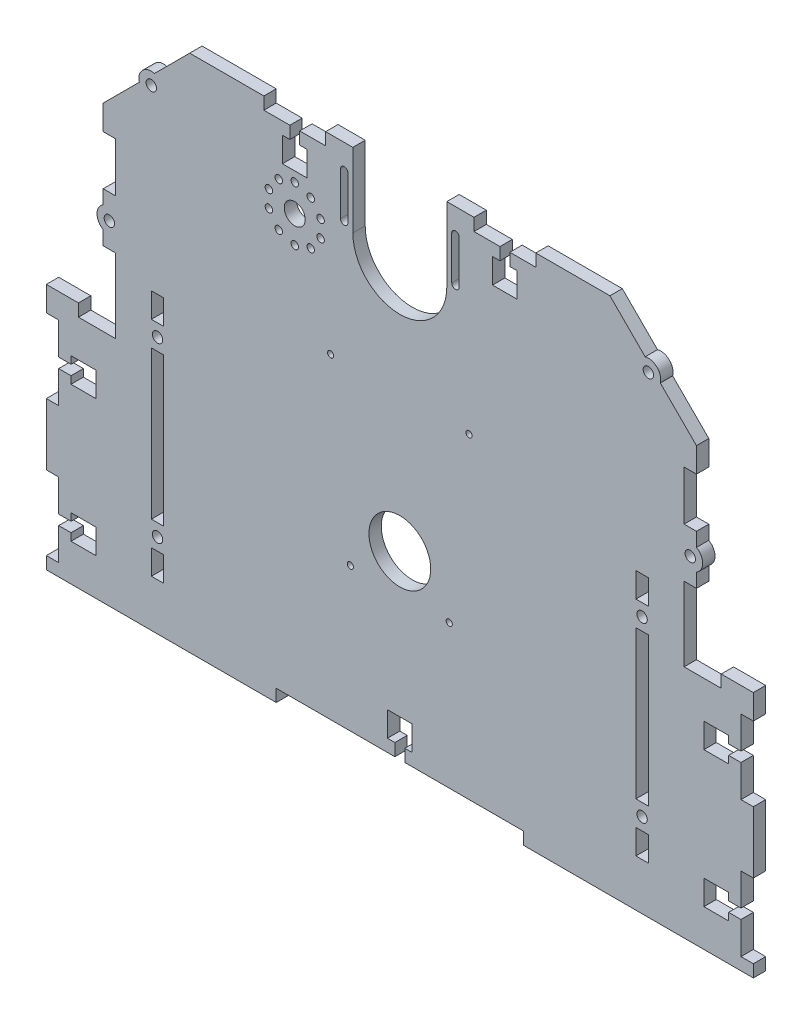
SolidWorks part; units mm, degrees
ref_plane "Front Plane" through (0, 0, 0) normal (0, 0, 1) x (1, 0, 0)
ref_plane "Top Plane" through (0, 0, 0) normal (0, 1, 0) x (1, 0, 0)
ref_plane "Right Plane" through (0, 0, 0) normal (1, 0, 0) x (0, 0, -1)
sketch "Sketch1" plane through (0, 0, 0) normal (0, 0, 1) x (1, 0, 0)
  line L1 (0, 0) -> (-240, 0)
  line L2 (0, 0) -> (0, 210)
  line L3 (0, 210) -> (-240, 210)
  line L4 (-240, 0) -> (-240, 210)
  dimension "D1" = 210
  dimension "D2" = 240
extrude "Boss-Extrude1" add sketch "Sketch1" along normal blind 5
sketch "Sketch2" plane through (0, 0, 5) normal (0, 0, 1) x (1, 0, 0)
  line L1 (-215.5, 19) -> (-220.5, 19)
  line L2 (-215.5, 19) -> (-215.5, 29)
  line L3 (-215.5, 29) -> (-220.5, 29)
  line L4 (-220.5, 19) -> (-220.5, 29)
  line L5 (-215.5, 39) -> (-220.5, 39)
  line L6 (-215.5, 39) -> (-215.5, 99)
  line L7 (-215.5, 99) -> (-220.5, 99)
  line L8 (-220.5, 39) -> (-220.5, 99)
  line L9 (-215.5, 109) -> (-220.5, 109)
  line L10 (-215.5, 109) -> (-215.5, 119)
  line L11 (-215.5, 119) -> (-220.5, 119)
  line L12 (-220.5, 109) -> (-220.5, 119)
  line L13 (-240, 210) -> (-240, 0) construction
  line L14 (-240, 0) -> (0, 0) construction
  line L15 (-200.5, 19) -> (-200.5, 29)
  line L16 (-200.5, 19) -> (-205.5, 19)
  line L17 (-205.5, 19) -> (-205.5, 29)
  line L18 (-200.5, 29) -> (-205.5, 29)
  line L19 (-200.5, 39) -> (-200.5, 99)
  line L20 (-205.5, 39) -> (-205.5, 99)
  line L21 (-200.5, 39) -> (-205.5, 39)
  line L22 (-200.5, 99) -> (-205.5, 99)
  line L23 (-200.5, 109) -> (-200.5, 119)
  line L24 (-200.5, 109) -> (-205.5, 109)
  line L25 (-205.5, 109) -> (-205.5, 119)
  line L26 (-200.5, 119) -> (-205.5, 119)
  line L27 (-120, 0) -> (-120, 45.6078) construction
  line L28 (-39.5, 119) -> (-34.5, 119)
  line L29 (-34.5, 109) -> (-34.5, 119)
  line L30 (-39.5, 109) -> (-34.5, 109)
  line L31 (-39.5, 109) -> (-39.5, 119)
  line L32 (-39.5, 99) -> (-34.5, 99)
  line L33 (-39.5, 39) -> (-34.5, 39)
  line L34 (-34.5, 39) -> (-34.5, 99)
  line L35 (-39.5, 39) -> (-39.5, 99)
  line L36 (-39.5, 29) -> (-34.5, 29)
  line L37 (-34.5, 19) -> (-34.5, 29)
  line L38 (-39.5, 19) -> (-34.5, 19)
  line L39 (-39.5, 19) -> (-39.5, 29)
  line L40 (-19.5, 109) -> (-19.5, 119)
  line L41 (-24.5, 119) -> (-19.5, 119)
  line L42 (-24.5, 109) -> (-24.5, 119)
  line L43 (-24.5, 109) -> (-19.5, 109)
  line L44 (-19.5, 39) -> (-19.5, 99)
  line L45 (-24.5, 99) -> (-19.5, 99)
  line L46 (-24.5, 39) -> (-24.5, 99)
  line L47 (-24.5, 39) -> (-19.5, 39)
  line L48 (-19.5, 19) -> (-19.5, 29)
  line L49 (-24.5, 29) -> (-19.5, 29)
  line L50 (-24.5, 19) -> (-24.5, 29)
  line L51 (-24.5, 19) -> (-19.5, 19)
  dimension "D1" = 5
  dimension "D2" = 10
  dimension "D3" = 60
  dimension "D4" = 10
  dimension "D5" = 5
  dimension "D6" = 5
  dimension "D7" = 19.5
  dimension "D8" = 119
  dimension "D9" = 10
  dimension "D10" = 10
  dimension "D11" = 2
extrude "Cut-Extrude1" cut sketch "Sketch2" against normal blind 5
sketch "Sketch3" plane through (0, 0, 5) normal (0, 0, 1) x (1, 0, 0)
  line L0 (-240, 210) -> (-240, 0) construction
  line L1 (0, 210) -> (-240, 210) construction
  line B0 (-120, 210) -> (-120, 177.73) construction
  line B1 (-240, 205) -> (-240, 185)
  line B2 (-240, 205) -> (-235, 205)
  line B3 (-240, 185) -> (-235, 185)
  line B4 (-235, 205) -> (-235, 185)
  line B5 (-240, 165) -> (-240, 145)
  line B6 (-240, 165) -> (-235, 165)
  line B7 (-235, 165) -> (-235, 145)
  line B8 (-240, 145) -> (-235, 145)
  line B9 (-235, 125) -> (-240, 125)
  line B10 (-235, 125) -> (-235, 100)
  line B11 (-235, 100) -> (-240, 100)
  line B12 (-240, 125) -> (-240, 100)
  line B13 (0, 125) -> (0, 100)
  line B14 (-5, 100) -> (0, 100)
  line B15 (-5, 125) -> (-5, 100)
  line B16 (-5, 125) -> (0, 125)
  line B17 (0, 145) -> (-5, 145)
  line B18 (-5, 165) -> (-5, 145)
  line B19 (0, 165) -> (-5, 165)
  line B20 (0, 165) -> (0, 145)
  line B21 (-5, 205) -> (-5, 185)
  line B22 (0, 185) -> (-5, 185)
  line B23 (0, 205) -> (-5, 205)
  line B24 (0, 205) -> (0, 185)
  dimension "D1" = 5
  dimension "D2" = 5
sketch_block_instance "Block2-1"
sketch_block "Block2" parameters "D1"=5, "D2"=20, "D3"=25, "D4"=20, "D5"=20, "D6"=5
extrude "Cut-Extrude2" cut sketch "Sketch3" against normal blind 10
sketch "Sketch4" plane through (0, 0, 5) normal (0, 0, 1) x (1, 0, 0)
  line L3 (0, 210) -> (-240, 210) construction
  line L5 (-120, 210) -> (-120, 170.8139) construction
  line L9 (-210, 205) -> (-235, 205)
  line L10 (-235, 205) -> (-235, 180)
  line L11 (-235, 180) -> (-210, 205)
  line L12 (-240, 185) -> (-240, 165) construction
  line L13 (-210, 205) -> (-205, 210)
  line L14 (-205, 210) -> (-240, 210)
  line L15 (-240, 210) -> (-240, 175)
  line L16 (-235, 180) -> (-240, 175)
  line L17 (-5, 180) -> (0, 175)
  line L18 (0, 210) -> (0, 175)
  line L19 (-35, 210) -> (0, 210)
  line L20 (-30, 205) -> (-35, 210)
  line L21 (-5, 180) -> (-30, 205)
  line L22 (-5, 205) -> (-5, 180)
  line L23 (-30, 205) -> (-5, 205)
  dimension "D1" = 25
  dimension "D2" = 25
  dimension "D3" = 5
  dimension "D4" = 5
extrude "Cut-Extrude3" cut sketch "Sketch4" against normal blind 10 contours L16 L10 L9 L13 L14 L15 | L10 L11 L9 | L23 L21 L22 | L20 L23 L22 L17 L18 L19
sketch "Sketch5" plane through (0, 0, 5) normal (0, 0, 1) x (1, 0, 0)
  line L0 (-35, 210) -> (-205, 210) construction
  line L1 (-175, 210) -> (-150, 210)
  line L2 (-175, 210) -> (-175, 205)
  line L3 (-175, 205) -> (-150, 205)
  line L4 (-150, 210) -> (-150, 205)
  line L5 (-120, 210) -> (-120, 191.0501) construction
  line L6 (-65, 205) -> (-90, 205)
  line L7 (-90, 210) -> (-90, 205)
  line L8 (-65, 210) -> (-90, 210)
  line L9 (-65, 210) -> (-65, 205)
  dimension "D1" = 5
  dimension "D2" = 25
  dimension "D3" = 30
extrude "Cut-Extrude4" cut sketch "Sketch5" against normal blind 10
sketch "Sketch7" plane through (0, 0, 5) normal (0, 0, 1) x (1, 0, 0)
  line L0 (-205.5, 39) -> (-200.5, 39) construction
  line L1 (-200.5, 39) -> (-200.5, 99) construction
  line L2 (-203, 34) -> (-218, 34) construction
  line L3 (-210.5, 34) -> (-210.5, 46.7899) construction
  line L4 (-215.5, 69) -> (-205.5, 69) construction
  line L5 (-215.5, 39) -> (-215.5, 99) construction
  line L6 (-205.5, 99) -> (-205.5, 39) construction
  line L7 (-120, 0) -> (-120, 30.8052) construction
  line L8 (-240, 0) -> (0, 0) construction
  line L9 (-24.5, 69) -> (-34.5, 69) construction
  line L10 (-29.5, 34) -> (-29.5, 46.7899) construction
  line L11 (-37, 34) -> (-22, 34) construction
  circle A0 centre (-203, 34) radius 2.1
  circle A1 centre (-218, 34) radius 2.1
  circle A2 centre (-203, 104) radius 2.1
  circle A3 centre (-218, 104) radius 2.1
  circle A4 centre (-22, 104) radius 2.1
  circle A5 centre (-37, 104) radius 2.1
  circle A6 centre (-22, 34) radius 2.1
  circle A7 centre (-37, 34) radius 2.1
  dimension "D1" = 4.2
  dimension "D2" = 5
  dimension "D3" = 2.5
extrude "Cut-Extrude6" cut sketch "Sketch7" against normal blind 5
sketch "Sketch8" plane through (0, 0, 5) normal (0, 0, 1) x (1, 0, 0)
  line L0 (-124.3301, 210) -> (-115.6699, 210)
  line L2 (-54.3301, 210) -> (-45.6699, 210)
  line L3 (-194.3301, 210) -> (-185.6699, 210)
  line L4 (0, 0) -> (0, 100) construction
  line L5 (-240, 0) -> (0, 0) construction
  arc A1 (-115.6699, 210) -> (-124.3301, 210) centre (-120, 207.5) ccw
  arc A2 (-45.6699, 210) -> (-54.3301, 210) centre (-50, 207.5) ccw
  arc A3 (-185.6699, 210) -> (-194.3301, 210) centre (-190, 207.5) ccw
  dimension "D1" = 45.6699
  dimension "D2" = 10
  dimension "D3" = 50
  dimension "D4" = 115.6699
  dimension "D5" = 185.6699
  dimension "D6" = 207.5
extrude "Boss-Extrude2" add sketch "Sketch8" against normal blind 5
sketch "Sketch9" plane through (0, 0, 5) normal (0, 0, 1) x (1, 0, 0)
  line L0 (-120, 212.5) -> (-120, 198.1441) construction
  circle A0 centre (-50, 207.5) radius 2.1
  arc A1 (-115.6699, 210) -> (-124.3301, 210) centre (-120, 207.5) ccw construction
  circle A2 centre (-120, 207.5) radius 2.1
  circle A3 centre (-190, 207.5) radius 2.1
  dimension "D1" = 4.2
  dimension "D2" = 4.2
extrude "Cut-Extrude7" cut sketch "Sketch9" against normal blind 5
sketch "Sketch10" plane through (0, 0, 5) normal (0, 0, 1) x (1, 0, 0)
  line L0 (-205, 210) -> (-240, 175) construction
  line L1 (-222.305, 192.695) -> (-212.586, 182.9761) construction
  line L2 (-115.6699, 210) -> (-124.3301, 210) construction
  line L3 (-120, 210) -> (-120, 185.6797) construction
  line L4 (-17.695, 192.695) -> (-27.414, 182.9761) construction
  circle A0 centre (-220.5372, 190.9273) radius 2.1
  circle A1 centre (-19.4628, 190.9273) radius 2.1
  dimension "D1" = 4.2
  dimension "D2" = 2.5
extrude "Cut-Extrude8" cut sketch "Sketch10" against normal blind 5
sketch "Sketch11" plane through (0, 0, 5) normal (0, 0, 1) x (1, 0, 0)
  line L0 (-205, 210) -> (-240, 175) construction
  line L1 (-219.2431, 195.7569) -> (-225.3668, 189.6332)
  line L2 (-90, 205) -> (-150, 205) construction
  line L3 (-120, 205) -> (-120, 186.0831) construction
  line L4 (-20.7569, 195.7569) -> (-14.6332, 189.6332)
  arc A0 (-219.2431, 195.7569) -> (-225.3668, 189.6332) centre (-220.5372, 190.9273) ccw
  arc A1 (-20.7569, 195.7569) -> (-14.6332, 189.6332) centre (-19.4628, 190.9273) cw
  dimension "D1" = 5
extrude "Boss-Extrude3" add sketch "Sketch11" against normal blind 5
sketch "Sketch13" plane through (0, 0, 5) normal (0, 0, 1) x (1, 0, 0)
  line L0 (-235, 125) -> (-240, 125) construction
  line L1 (-240, 145) -> (-240, 125) construction
  line L2 (-120, 207.5) -> (-120, 177.5095) construction
  circle A0 centre (-237.5, 135) radius 2.1
  circle A1 centre (-2.5, 135) radius 2.1
  dimension "D1" = 4.2
  dimension "D2" = 10
  dimension "D3" = 2.5
extrude "Cut-Extrude9" cut sketch "Sketch13" against normal blind 5
sketch "Sketch14" plane through (0, 0, 5) normal (0, 0, 1) x (1, 0, 0)
  line L0 (0, 0) -> (0, 100) construction
  line L1 (-240, 0) -> (0, 0) construction
  circle A4 centre (-92, 133) radius 1.25
  circle A5 centre (-100, 63) radius 1.25
  circle A6 centre (-148, 133) radius 1.25
  circle A7 centre (-140, 63) radius 1.25
  dimension "D1" = 2.5
  dimension "D2" = 92
  dimension "D3" = 100
  dimension "D4" = 140
  dimension "D5" = 148
  dimension "D6" = 63
  dimension "D7" = 133
extrude "Cut-Extrude10" cut sketch "Sketch14" against normal blind 5
sketch "Sketch22" plane through (0, 0, 5) normal (0, 0, 1) x (1, 0, 0)
  line L0 (-120, 209.6) -> (-120, 181.3792) construction
  line L1 (-124.3301, 210) -> (-150, 210) construction
  circle A0 centre (-120, 207.5) radius 2.1 construction
  circle A1 centre (-120, 180) radius 19
  dimension "D1" = 38
  dimension "D2" = 30
extrude "Cut-Extrude16" cut sketch "Sketch22" against normal blind 5
sketch "Sketch23" plane through (0, 0, 5) normal (0, 0, 1) x (1, 0, 0)
  line L1 (-240, 145) -> (-240, 125) construction
  line L2 (-240, 130.6699) -> (-240, 139.3301)
  line L3 (-120, 207.5) -> (-120, 197.1614) construction
  line L4 (0, 130.6699) -> (0, 139.3301)
  line L5 (0, 0) -> (0, 100) construction
  line L6 (-240, 0) -> (0, 0) construction
  arc A0 (-240, 139.3301) -> (-240, 130.6699) centre (-237.5, 135) ccw
  arc A1 (0, 139.3301) -> (0, 130.6699) centre (-2.5, 135) cw
  dimension "D1" = 5
  dimension "D2" = 2.5
  dimension "D3" = 130.6699
extrude "Boss-Extrude4" add sketch "Sketch23" against normal blind 5
sketch "Sketch26" plane through (0, 0, 5) normal (0, 0, 1) x (1, 0, 0)
  line L0 (0, 100) -> (23, 100)
  line L1 (0, 0) -> (0, 100) construction
  line L2 (23, 100) -> (23, -6)
  line L3 (23, -6) -> (-17, -6)
  line L4 (-17, -6) -> (-17, 0)
  line L5 (-240, 0) -> (0, 0) construction
  line L6 (0, 100) -> (0, 0)
  line L7 (0, 0) -> (-17, 0)
  line L8 (-120, 0) -> (-120, 18.176) construction
  line L9 (-240, 0) -> (-223, 0)
  line L10 (-240, 100) -> (-240, 0)
  line L11 (-223, -6) -> (-223, 0)
  line L12 (-263, -6) -> (-223, -6)
  line L13 (-263, 100) -> (-263, -6)
  line L14 (-240, 100) -> (-263, 100)
  line L15 (0, 0) -> (23, 0)
  line L16 (-240, 0) -> (-263, 0)
  dimension "D1" = 23
  dimension "D2" = 106
  dimension "D3" = 6
  dimension "D4" = 40
extrude "Boss-Extrude5" add sketch "Sketch26" against normal blind 5 contours L6 L15 L2 L0 | L16 L10 L14 L13
sketch "Sketch27" plane through (0, 0, 5) normal (0, 0, 1) x (1, 0, 0)
  line L1 (23, 90) -> (18, 90)
  line L2 (23, 90) -> (23, 60)
  line L3 (23, 60) -> (18, 60)
  line L4 (18, 90) -> (18, 60)
  line L6 (23, 35) -> (18, 35)
  line L7 (23, 35) -> (23, 5)
  line L8 (23, 5) -> (18, 5)
  line L9 (18, 35) -> (18, 5)
  line L10 (-263, 100) -> (-263, 0) construction
  line L11 (-120, 0) -> (-120, 32.5567) construction
  line L12 (-263, 0) -> (23, 0) construction
  line L13 (-258, 35) -> (-258, 5)
  line L14 (-263, 5) -> (-258, 5)
  line L15 (-263, 35) -> (-263, 5)
  line L16 (-263, 35) -> (-258, 35)
  line L17 (-258, 90) -> (-258, 60)
  line L18 (-263, 60) -> (-258, 60)
  line L19 (-263, 90) -> (-263, 60)
  line L20 (-263, 90) -> (-258, 90)
  line L21 (-263, 0) -> (23, 0) construction
  circle A0 centre (20.5, 47.5) radius 2.1
  circle A1 centre (-260.5, 47.5) radius 2.1
  dimension "D6" = 4.2
  dimension "D8" = 12.5
  dimension "D1" = 30
  dimension "D2" = 30
  dimension "D3" = 5
  dimension "D4" = 25
extrude "Cut-Extrude19" cut sketch "Sketch27" against normal blind 5 contours L20 L19 L18 L17 | L16 L15 L14 L13 | L1 L4 L3 L2 | L6 L9 L8 L7
sketch "Sketch28" plane through (0, 0, 5) normal (0, 0, 1) x (1, 0, 0)
  line L1 (23, 43.1699) -> (23, 51.8301)
  line L2 (-120, 0) -> (-120, 20.2272) construction
  line L3 (-263, 0) -> (23, 0) construction
  line L4 (-263, 43.1699) -> (-263, 51.8301)
  arc A0 (23, 51.8301) -> (23, 43.1699) centre (20.5, 47.5) cw
  arc A1 (-263, 51.8301) -> (-263, 43.1699) centre (-260.5, 47.5) ccw
  dimension "D1" = 5
extrude "Boss-Extrude6" [suppressed] add sketch "Sketch28" against normal blind 5
sketch "Sketch29" plane through (0, 0, 5) normal (0, 0, 1) x (1, 0, 0)
  line L0 (-120, 0) -> (-120, 23.9955) construction
  line L1 (-240, 95) -> (-235, 95)
  line L2 (-240, 95) -> (-240, 100)
  line L3 (-240, 100) -> (-235, 100)
  line L4 (-235, 95) -> (-235, 100)
  line L5 (-263, 0) -> (23, 0) construction
  line L6 (-5, 95) -> (-5, 100)
  line L7 (0, 100) -> (-5, 100)
  line L8 (0, 95) -> (0, 100)
  line L9 (0, 95) -> (-5, 95)
  dimension "D1" = 5
  dimension "D2" = 5
extrude "Cut-Extrude20" cut sketch "Sketch29" against normal blind 5
sketch "Sketch31" plane through (0, 100, 0) normal (0, 1, 0) x (1, 0, 0)
  line L1 (-240, 0) -> (-250, 0)
  line L2 (-240, 0) -> (-240, -5)
  line L3 (-240, -5) -> (-250, -5)
  line L4 (-250, 0) -> (-250, -5)
  dimension "D1" = 10
extrude "Cut-Extrude21" cut sketch "Sketch31" against normal blind 5
ref_plane "Plane1" through (-120, 0, 0) normal (-1, 0, 0) x (0, 0, 1)
mirror "Mirror2" about plane through (-120, 0, 0) normal (-1, 0, 0) of "Cut-Extrude21"
sketch "Sketch32" plane through (0, 0, 0) normal (0, -1, 0) x (1, 0, 0)
  line L4 (23, 5) -> (-263, 5)
  line L5 (23, 0) -> (23, 5)
  line L6 (-263, 0) -> (23, 0)
  line L8 (23, 5) -> (-263, 5)
  line L10 (-263, 0) -> (23, 0)
  line L16 (23, 0) -> (23, 5)
  line L18 (-263, 5) -> (-263, 0)
  line L19 (-263, 5) -> (-263, 0)
  dimension "D1" = 0
extrude "Boss-Extrude7" add sketch "Sketch32" along normal blind 1
sketch "Sketch33" plane through (0, -1, 0) normal (0, -1, 0) x (1, 0, 0)
  line L4 (23, 0) -> (23, 5)
  line L5 (23, 5) -> (-263, 5)
  line L6 (-263, 5) -> (-263, 0)
  line L7 (-263, 0) -> (23, 0)
  line L8 (23, 0) -> (23, 5)
  line L9 (23, 5) -> (-263, 5)
  line L10 (-263, 5) -> (-263, 0)
  line L11 (-263, 0) -> (23, 0)
  dimension "D1" = 0
extrude "Cut-Extrude22" cut sketch "Sketch33" against normal blind 1
sketch "Sketch35" plane through (0, 0, 5) normal (0, 0, 1) x (1, 0, 0)
  line L0 (18, 35) -> (18, 5) construction
  line L1 (18, 18) -> (13, 18)
  line L2 (18, 18) -> (18, 22)
  line L3 (18, 22) -> (13, 22)
  line L4 (13, 18) -> (13, 22)
  line L5 (-120, 0) -> (-120, 26.557) construction
  line L6 (13, 15) -> (3, 15)
  line L7 (13, 15) -> (13, 25)
  line L8 (13, 25) -> (3, 25)
  line L9 (3, 15) -> (3, 25)
  line L10 (23, 0) -> (-263, 0) construction
  line L11 (-243, 15) -> (-243, 25)
  line L12 (-253, 25) -> (-243, 25)
  line L13 (-253, 15) -> (-253, 25)
  line L14 (-253, 15) -> (-243, 15)
  line L15 (-253, 18) -> (-253, 22)
  line L16 (-258, 22) -> (-253, 22)
  line L17 (-258, 18) -> (-258, 22)
  line L18 (-258, 18) -> (-253, 18)
  line L19 (25.5, 47.5) -> (14.6629, 47.5) construction
  line L21 (-258, 77) -> (-253, 77)
  line L22 (-258, 77) -> (-258, 73)
  line L23 (-258, 73) -> (-253, 73)
  line L24 (-253, 77) -> (-253, 73)
  line L25 (-253, 80) -> (-243, 80)
  line L26 (-253, 80) -> (-253, 70)
  line L27 (-253, 70) -> (-243, 70)
  line L28 (-243, 80) -> (-243, 70)
  line L29 (3, 80) -> (3, 70)
  line L30 (13, 70) -> (3, 70)
  line L31 (13, 80) -> (13, 70)
  line L32 (13, 80) -> (3, 80)
  line L33 (13, 77) -> (13, 73)
  line L34 (18, 73) -> (13, 73)
  line L35 (18, 77) -> (18, 73)
  line L36 (18, 77) -> (13, 77)
  point P10 (13, 20)
  point P11 (18, 20)
  point P12 (18, 20)
  dimension "D1" = 5
  dimension "D2" = 5
  dimension "D3" = 10
  dimension "D4" = 10
  dimension "D5" = 4
extrude "Cut-Extrude24" cut sketch "Sketch35" against normal blind 5 contours L7 L1 L2 L3 | L9 L1 L7 L3 | L1 L9 L3 L4 | L9 L3 L7 L8 | L9 L6 L7 L1 | L31 L36 L29 L34 | L29 L36 L33 L34 | L36 L31 L32 L29 | L31 L34 L29 L30 | L35 L36 L31 L34 | L17 L18 L13 L16 | L13 L18 L11 L16 | L13 L16 L11 L12 | L18 L13 L14 L11 | L11 L18 L15 L16 | L28 L21 L26 L23 | L26 L21 L22 L23 | L28 L25 L26 L21 | L28 L23 L26 L27 | L21 L28 L23 L24
sketch "Sketch37" plane through (0, 0, 5) normal (0, 0, 1) x (1, 0, 0)
  line L0 (-194.3301, 210) -> (-185.6699, 210)
  line L1 (-124.3301, 210) -> (-115.6699, 210)
  line L2 (-54.3301, 210) -> (-45.6699, 210)
  arc A0 (-185.6699, 210) -> (-194.3301, 210) centre (-190, 207.5) ccw construction
  arc A1 (-115.6699, 210) -> (-124.3301, 210) centre (-120, 207.5) ccw construction
  arc A2 (-45.6699, 210) -> (-54.3301, 210) centre (-50, 207.5) ccw construction
  arc A3 (-185.6699, 210) -> (-194.3301, 210) centre (-190, 207.5) ccw
  arc A4 (-115.6699, 210) -> (-124.3301, 210) centre (-120, 207.5) ccw
  arc A5 (-45.6699, 210) -> (-54.3301, 210) centre (-50, 207.5) ccw
  circle A6 centre (-190, 207.5) radius 2.1
  circle A7 centre (-120, 207.5) radius 2.1
  circle A8 centre (-50, 207.5) radius 2.1
extrude "Cut-Extrude25" cut sketch "Sketch37" against normal blind 5
sketch "Sketch38" plane through (0, 0, 5) normal (0, 0, 1) x (1, 0, 0)
  circle A0 centre (-190, 207.5) radius 2.1 construction
  circle A1 centre (-120, 207.5) radius 2.1 construction
  circle A2 centre (-50, 207.5) radius 2.1 construction
  circle A3 centre (-190, 207.5) radius 2.1
  circle A4 centre (-120, 207.5) radius 2.1
  circle A5 centre (-50, 207.5) radius 2.1
extrude "Boss-Extrude8" add sketch "Sketch38" against normal blind 5
sketch "Sketch39" plane through (0, 0, 5) normal (0, 0, 1) x (1, 0, 0)
  line L0 (-175, 205) -> (-150, 205) construction
  line L1 (-160.5, 205) -> (-164.5, 205)
  line L2 (-160.5, 205) -> (-160.5, 200)
  line L3 (-160.5, 200) -> (-164.5, 200)
  line L4 (-164.5, 205) -> (-164.5, 200)
  line L5 (-120, 210) -> (-120, 200.9162) construction
  line L6 (-157.5, 190) -> (-167.5, 190)
  line L7 (-157.5, 190) -> (-157.5, 200)
  line L8 (-157.5, 200) -> (-167.5, 200)
  line L9 (-167.5, 190) -> (-167.5, 200)
  line L10 (-90, 210) -> (-150, 210) construction
  line L11 (-72.5, 190) -> (-72.5, 200)
  line L12 (-82.5, 200) -> (-72.5, 200)
  line L13 (-82.5, 190) -> (-82.5, 200)
  line L14 (-82.5, 190) -> (-72.5, 190)
  line L15 (-75.5, 205) -> (-75.5, 200)
  line L16 (-79.5, 200) -> (-75.5, 200)
  line L17 (-79.5, 205) -> (-79.5, 200)
  line L18 (-79.5, 205) -> (-75.5, 205)
  point P10 (-162.5, 190)
  point P11 (-162.5, 200)
  point P12 (-162.5, 205)
  point P13 (-162.5, 205)
  dimension "D1" = 10
  dimension "D2" = 4
  dimension "D3" = 10
  dimension "D4" = 5
  dimension "D5" = 5
extrude "Cut-Extrude26" cut sketch "Sketch39" against normal blind 5 contours L14 L11 L12 L13 | L16 L15 L18 L17 | L3 L4 L1 L2 | L7 L8 L9 L6
sketch "Sketch40" plane through (0, 0, 0) normal (0, -1, 0) x (1, 0, 0)
  line L0 (-263, 0) -> (23, 0) construction
  line L1 (-170, 0) -> (-70, 0)
  line L2 (-170, 0) -> (-170, 5)
  line L3 (-170, 5) -> (-70, 5)
  line L4 (-70, 0) -> (-70, 5)
  line L5 (23, 5) -> (-263, 5) construction
  line L6 (23, 0) -> (23, 5) construction
  dimension "D1" = 100
  dimension "D2" = 93
extrude "Cut-Extrude27" cut sketch "Sketch40" against normal blind 5
sketch "Sketch41" plane through (0, 0, 5) normal (0, 0, 1) x (1, 0, 0)
  line L0 (-39.5, 29) -> (-39.5, 19) construction
  line L1 (-39.5, 19) -> (-34.5, 19) construction
  line L2 (-34.5, 19) -> (-34.5, 29) construction
  line L3 (-34.5, 29) -> (-39.5, 29) construction
  line L4 (-39.5, 39) -> (-34.5, 39) construction
  line L5 (-34.5, 39) -> (-34.5, 99) construction
  line L6 (-39.5, 99) -> (-39.5, 39) construction
  line L7 (-34.5, 99) -> (-39.5, 99) construction
  line L8 (-34.5, 109) -> (-34.5, 119) construction
  line L9 (-39.5, 109) -> (-34.5, 109) construction
  line L10 (-39.5, 119) -> (-39.5, 109) construction
  line L11 (-34.5, 119) -> (-39.5, 119) construction
  line L12 (-200.5, 119) -> (-205.5, 119) construction
  line L13 (-205.5, 119) -> (-205.5, 109) construction
  line L14 (-200.5, 109) -> (-200.5, 119) construction
  line L15 (-205.5, 109) -> (-200.5, 109) construction
  line L16 (-200.5, 99) -> (-205.5, 99) construction
  line L17 (-200.5, 39) -> (-200.5, 99) construction
  line L18 (-205.5, 99) -> (-205.5, 39) construction
  line L19 (-205.5, 39) -> (-200.5, 39) construction
  line L20 (-200.5, 29) -> (-205.5, 29) construction
  line L21 (-200.5, 19) -> (-200.5, 29) construction
  line L22 (-205.5, 19) -> (-200.5, 19) construction
  line L23 (-205.5, 29) -> (-205.5, 19) construction
  line L24 (-39.5, 29) -> (-39.5, 19)
  line L25 (-39.5, 19) -> (-34.5, 19)
  line L26 (-34.5, 19) -> (-34.5, 29)
  line L27 (-34.5, 29) -> (-39.5, 29)
  line L28 (-39.5, 39) -> (-34.5, 39)
  line L29 (-34.5, 39) -> (-34.5, 99)
  line L30 (-39.5, 99) -> (-39.5, 39)
  line L31 (-34.5, 99) -> (-39.5, 99)
  line L32 (-34.5, 109) -> (-34.5, 119)
  line L33 (-39.5, 109) -> (-34.5, 109)
  line L34 (-39.5, 119) -> (-39.5, 109)
  line L35 (-34.5, 119) -> (-39.5, 119)
  line L36 (-200.5, 119) -> (-205.5, 119)
  line L37 (-205.5, 119) -> (-205.5, 109)
  line L38 (-200.5, 109) -> (-200.5, 119)
  line L39 (-205.5, 109) -> (-200.5, 109)
  line L40 (-200.5, 99) -> (-205.5, 99)
  line L41 (-200.5, 39) -> (-200.5, 99)
  line L42 (-205.5, 99) -> (-205.5, 39)
  line L43 (-205.5, 39) -> (-200.5, 39)
  line L44 (-200.5, 29) -> (-205.5, 29)
  line L45 (-200.5, 19) -> (-200.5, 29)
  line L46 (-205.5, 19) -> (-200.5, 19)
  line L47 (-205.5, 29) -> (-205.5, 19)
  circle A0 centre (-37, 34) radius 2.1 construction
  circle A1 centre (-37, 104) radius 2.1 construction
  circle A2 centre (-203, 104) radius 2.1 construction
  circle A3 centre (-203, 34) radius 2.1 construction
  circle A4 centre (-37, 34) radius 2.1
  circle A5 centre (-37, 104) radius 2.1
  circle A6 centre (-203, 104) radius 2.1
  circle A7 centre (-203, 34) radius 2.1
extrude "Boss-Extrude9" add sketch "Sketch41" against normal blind 5
sketch "Sketch42" plane through (0, 0, 5) normal (0, 0, 1) x (1, 0, 0)
  line L0 (-139, 180) -> (-139, 210)
  line L1 (-90, 210) -> (-150, 210) construction
  line L2 (-101, 180) -> (-101, 210)
  line L3 (-101, 210) -> (-139, 210)
  circle A0 centre (-120, 180) radius 19 construction
  arc A1 (-101, 180) -> (-139, 180) centre (-120, 180) ccw
extrude "Cut-Extrude28" cut sketch "Sketch42" against normal blind 5
sketch "Sketch43" plane through (0, 0, 5) normal (0, 0, 1) x (1, 0, 0)
  line L0 (-70, 5) -> (-170, 5) construction
  line L1 (-122, 5) -> (-118, 5)
  line L2 (-122, 5) -> (-122, 10)
  line L3 (-122, 10) -> (-118, 10)
  line L4 (-118, 5) -> (-118, 10)
  line L6 (-125, 10) -> (-115, 10)
  line L7 (-125, 10) -> (-125, 20)
  line L8 (-125, 20) -> (-115, 20)
  line L9 (-115, 10) -> (-115, 20)
  point P10 (-120, 20)
  point P11 (-120, 5)
  point P12 (-120, 5)
  dimension "D1" = 5
  dimension "D2" = 10
  dimension "D3" = 10
  dimension "D4" = 4
extrude "Cut-Extrude29" cut sketch "Sketch43" against normal blind 5 contours L6 L9 L8 L7 L3 | L1 L4 L3 L2
sketch "Sketch44" plane through (0, 0, 5) normal (0, 0, 1) x (1, 0, 0)
  line L0 (-139, 210) -> (-139, 180) construction
  line L1 (-141, 182.5) -> (-144, 182.5)
  line L2 (-141, 182.5) -> (-141, 200)
  line L3 (-141, 200) -> (-144, 200)
  line L4 (-144, 182.5) -> (-144, 200)
  line L5 (-139, 210) -> (-150, 210) construction
  line L6 (-120, 161) -> (-120, 185.8219) construction
  line L7 (-96, 182.5) -> (-96, 200)
  line L8 (-99, 200) -> (-96, 200)
  line L9 (-99, 182.5) -> (-99, 200)
  line L10 (-99, 182.5) -> (-96, 182.5)
  line L11 (-157.5, 190) -> (-167.5, 190) construction
  line L12 (-157.5, 190) -> (-157.5, 200) construction
  arc A0 (-139, 180) -> (-101, 180) centre (-120, 180) ccw construction
  circle A1 centre (-142.5, 182.5) radius 1.5
  circle A2 centre (-142.5, 200) radius 1.5
  circle A3 centre (-97.5, 200) radius 1.5
  circle A4 centre (-97.5, 182.5) radius 1.5
  circle A5 centre (-162.5, 175) radius 4.25
  circle A6 centre (-162.5, 186) radius 1.5
  circle A7 centre (-156.0344, 183.8992) radius 1.5
  circle A8 centre (-152.0384, 178.3992) radius 1.5
  circle A9 centre (-152.0384, 171.6008) radius 1.5
  circle A10 centre (-156.0344, 166.1008) radius 1.5
  circle A11 centre (-162.5, 164) radius 1.5
  circle A12 centre (-168.9656, 166.1008) radius 1.5
  circle A13 centre (-172.9616, 171.6008) radius 1.5
  circle A14 centre (-172.9616, 178.3992) radius 1.5
  circle A15 centre (-168.9656, 183.8992) radius 1.5
  dimension "D5" = 8.5
  dimension "D6" = 15
  dimension "D7" = 5
  dimension "D8" = 11
  dimension "D9" = 3
  dimension "D1" = 2
  dimension "D2" = 3
  dimension "D3" = 10
  dimension "D4" = 17.5
  dimension "D10" = 10
extrude "Cut-Extrude30" cut sketch "Sketch44" against normal blind 10 contours A4 L7 A3 L9 | L10 A4 | L10 A4 | L8 A3 | L8 A3 | L1 A1 | L1 A1 | A2 L4 A1 L2 | L3 A2 | L3 A2 | A5 | A7 | A8 | A9 | A10 | A11 | A12 | A13 | A14 | A15 | A6
sketch "Sketch45" plane through (0, 0, 5) normal (0, 0, 1) x (1, 0, 0)
  circle A0 centre (-120, 78) radius 12.5
  circle A1 centre (-140, 63) radius 1.25 construction
  dimension "D1" = 20
  dimension "D2" = 15
  dimension "D3" = 25
extrude "Cut-Extrude31" cut sketch "Sketch45" against normal blind 10
